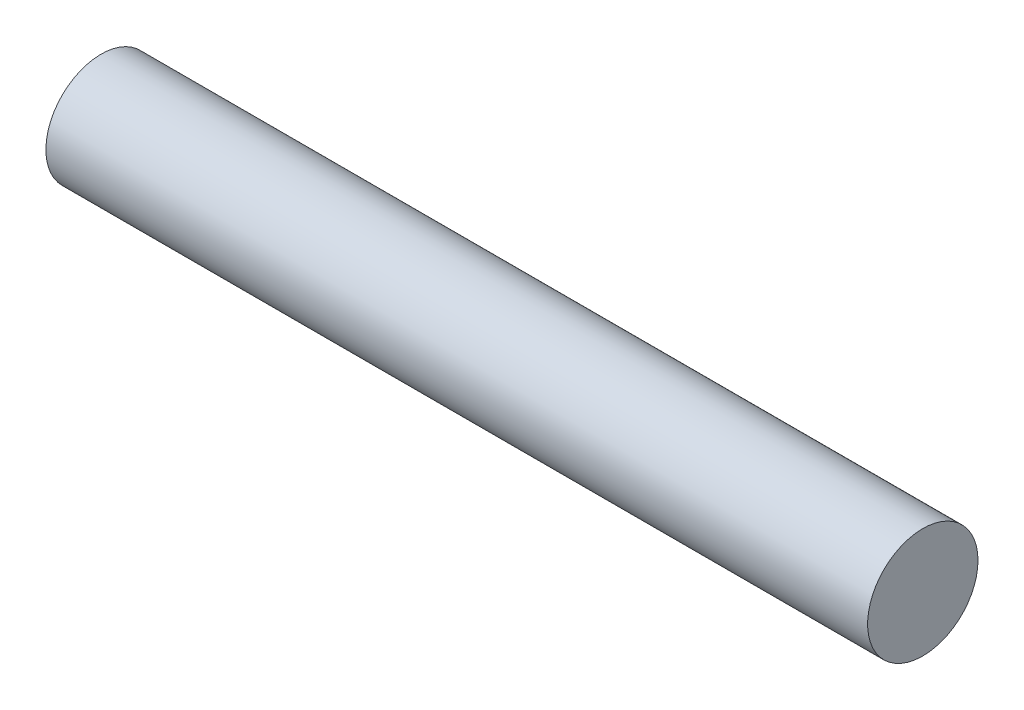
SolidWorks part; units mm, degrees
ref_plane "Front Plane" through (0, 0, 0) normal (0, 0, 1) x (1, 0, 0)
ref_plane "Top Plane" through (0, 0, 0) normal (0, 1, 0) x (1, 0, 0)
ref_plane "Right Plane" through (0, 0, 0) normal (1, 0, 0) x (0, 0, -1)
sketch "Sketch1" plane through (0, 0, 0) normal (1, 0, 0) x (0, 0, -1)
  circle A0 centre (0, 0) radius 6.35
  dimension "D1" = 12.7
extrude "Boss-Extrude1" add sketch "Sketch1" along normal offset from surface 1.5875 and the other way offset from surface (45.6875 mm away) 1.5875
sketch "Sketch3" plane through (45.6875, 0, 0) normal (1, 0, 0) x (0, 0, -1)
  circle A1 centre (0, 0) radius 6.35
  circle A2 centre (0, 0) radius 6.35
  dimension "D1" = 0
extrude "Boss-Extrude2" add sketch "Sketch3" along normal blind 3.175
sketch "Sketch2" plane through (0, 0, 0) normal (0, 0, 1) x (1, 0, 0)
  line L0 (0, 0) -> (48.8625, 0) construction
  line L1 (46.8559, 5.0292) -> (45.6875, 5.0292)
  line L2 (46.8559, 5.0292) -> (46.8559, 6.35)
  line L3 (46.8559, 6.35) -> (45.6875, 6.35)
  line L4 (45.6875, 5.0292) -> (45.6875, 6.35)
  line L6 (48.8625, 6.35) -> (-45.6875, 6.35) construction
  line L8 (48.8625, -6.35) -> (48.8625, 6.35) construction
  dimension "D1" = 1.1684
  dimension "D2" = 10.0584
  dimension "D3" = 3.175
revolve "Cut-Revolve1" [suppressed] cut sketch "Sketch2" angle 360 about L0
hole_wizard "1/4-20 Tapped Hole1" [suppressed] positions "Sketch8" profile "Sketch10" tap size "1/4-20" standard "ANSI Inch"
sketch "Sketch8" plane through (-44.1, 0, 0) normal (-1, 0, 0) x (0, 0, 1)
  point P0 (0, 0)
sketch "Sketch10" plane through (-44.1, 0, 0) normal (0, 1, 0) x (0, 0, 1)
  line L0 (0, 0) -> (0, 18.0438)
  line L1 (0, 18.0438) -> (2.5527, 16.51)
  line L2 (2.5527, 16.51) -> (2.5527, 0)
  line L5 (2.5527, 0) -> (0, 0)
  line L10 (0, 18.0438) -> (-2.5527, 16.51) construction
  line L11 (0, -6.35) -> (0, 107.95) construction
  dimension "Tap Drill Dia." = 5.1054
  dimension "Tap Drill Depth" = 16.51
  dimension "Drill Angle" = 118
cosmetic thread "Hole Thread1" [suppressed] parameters "D1"=12.7, "D2"=6.35
hole_wizard "1/8 (0.125) Diameter Hole1" [suppressed] positions "3DSketch3" profile "Sketch17" hole size "1/8" standard "ANSI Inch"
sketch3d "3DSketch3"
  point P7 (0, 0, 6.35)
sketch "Sketch17" plane through (0, 0, 6.35) normal (1, 0, 0) x (0, -1, 0)
  line L0 (0, 0) -> (0, 2.54)
  line L1 (0, 2.54) -> (1.5875, 1.5861)
  line L2 (1.5875, 1.5861) -> (1.5875, 0)
  line L5 (1.5875, 0) -> (0, 0)
  line L10 (0, 2.54) -> (-1.5875, 1.5861) construction
  line L11 (0, -6.35) -> (0, 107.95) construction
  dimension "Hole Dia." = 3.175
  dimension "Hole Depth" = 2.54
  dimension "Drill Angle" = 118
equation "\"ShaftDia\"=0.5"
equation "\"D1\"= \"YokeWidth\""
equation "\"EncoderWidth\"=0.125"
equation "\"D1@Boss-Extrude2\"=\"EncoderWidth\""
equation "\"D3@Sketch2\"=\"EncoderWidth\""
